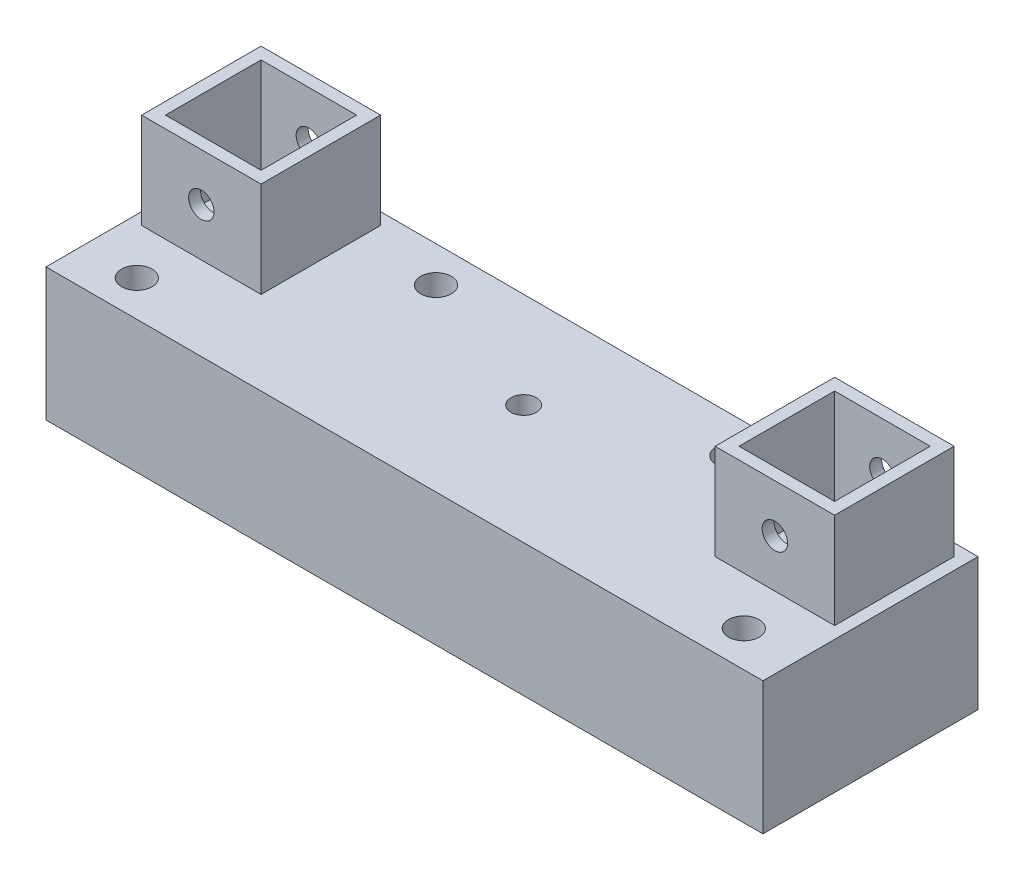
SolidWorks part; units mm, degrees
material "PPE"
ref_plane "Front Plane" through (0, 0, 0) normal (0, 0, 1) x (1, 0, 0)
ref_plane "Top Plane" through (0, 0, 0) normal (0, 1, 0) x (1, 0, 0)
ref_plane "Right Plane" through (0, 0, 0) normal (1, 0, 0) x (0, 0, -1)
sketch "Sketch1" plane through (0, 0, 0) normal (0, 1, 0) x (1, 0, 0)
  line L1 (-95.25, -28.575) -> (95.25, -28.575)
  line L2 (-95.25, -28.575) -> (-95.25, 28.575)
  line L3 (-95.25, 28.575) -> (95.25, 28.575)
  line L4 (95.25, -28.575) -> (95.25, 28.575)
  line L5 (-95.25, -28.575) -> (95.25, 28.575) construction
  line L6 (-95.25, 28.575) -> (95.25, -28.575) construction
  point P0 (0, 0)
  dimension "D1" = 190.5
  dimension "D2" = 57.15
extrude "Boss-Extrude1" add sketch "Sketch1" along normal blind 35.2298
sketch "Sketch2" plane through (0, 35.2298, 0) normal (0, 1, 0) x (1, 0, 0)
  line L1 (95.25, -28.575) -> (95.25, 28.575) construction
  line L2 (-95.25, -28.575) -> (95.25, -28.575) construction
  circle A0 centre (0, 3.0988) radius 3.3782
  dimension "D1" = 6.7564
  dimension "D2" = 95.25
  dimension "D3" = 31.6738
extrude "Cut-Extrude1" cut sketch "Sketch2" against normal blind 35.2298
sketch "Sketch3" plane through (0, 35.2298, 0) normal (0, 1, 0) x (1, 0, 0)
  line L1 (92.075, 25.4) -> (60.325, 25.4)
  line L2 (92.075, 25.4) -> (92.075, -6.35)
  line L3 (92.075, -6.35) -> (60.325, -6.35)
  line L4 (60.325, 25.4) -> (60.325, -6.35)
  line L5 (63.5, -3.175) -> (88.9, -3.175)
  line L6 (63.5, -3.175) -> (63.5, 22.225)
  line L7 (63.5, 22.225) -> (88.9, 22.225)
  line L8 (88.9, -3.175) -> (88.9, 22.225)
  line L10 (95.25, 28.575) -> (-95.25, 28.575) construction
  line L11 (95.25, -28.575) -> (95.25, 28.575) construction
  dimension "D1" = 31.75
  dimension "D2" = 31.75
  dimension "D3" = 25.4
  dimension "D4" = 25.4
  dimension "D5" = 3.175
  dimension "D6" = 3.175
  dimension "D7" = 3.175
  dimension "D8" = 3.175
extrude "Boss-Extrude2" add sketch "Sketch3" along normal blind 25.4
sketch "Sketch4" plane through (0, 0, -25.4) normal (0, 0, -1) x (-1, 0, 0)
  line L0 (-76.2, 60.6298) -> (-76.2, 35.2298) construction
  line L1 (-92.075, 60.6298) -> (-60.325, 60.6298) construction
  line L2 (-92.075, 35.2298) -> (-60.325, 35.2298) construction
  circle A0 centre (-76.2, 47.9298) radius 3.3782
  dimension "D1" = 6.7564
  dimension "D2" = 12.7
extrude "Cut-Extrude2" cut sketch "Sketch4" against normal through all
sketch "Sketch5" plane through (0, 0, 0) normal (0, -1, 0) x (1, 0, 0)
  line L0 (95.25, 28.575) -> (95.25, -28.575) construction
  line L1 (-95.25, 28.575) -> (95.25, 28.575) construction
  circle A0 centre (80.645, 19.05) radius 2.54
  circle A1 centre (39.243, -19.05) radius 2.54
  dimension "D6" = 5.08
  dimension "D1" = 14.605
  dimension "D2" = 9.525
  dimension "D4" = 47.625
  dimension "D5" = 56.007
extrude "Cut-Extrude3" cut sketch "Sketch5" against normal up to next (35.2298 mm away)
sketch "Sketch6" plane through (0, 35.2298, 0) normal (0, 1, 0) x (1, 0, 0)
  circle A0 centre (80.645, -19.05) radius 4.064
  circle A1 centre (39.243, 19.05) radius 4.064
  dimension "D1" = 8.128
extrude "Cut-Extrude4" cut sketch "Sketch6" against normal offset from surface (28.8798 mm away) 6.35 up to face at (80.645, 0, 16.51)
mirror "Mirror1" about plane through (0, 0, 0) normal (1, 0, 0) of "Cut-Extrude4", "Cut-Extrude3", "Boss-Extrude2", "Cut-Extrude2"
sketch "Sketch7" plane through (0, 0, 0) normal (0, -1, 0) x (1, 0, 0)
  line L0 (95.25, -28.575) -> (-95.25, -28.575) construction
  line L1 (6.5991, -3.0988) -> (3.2996, 2.6162)
  line L2 (3.2996, 2.6162) -> (-3.2996, 2.6162)
  line L3 (-3.2996, 2.6162) -> (-6.5991, -3.0988)
  line L4 (-6.5991, -3.0988) -> (-3.2996, -8.8138)
  line L5 (-3.2996, -8.8138) -> (3.2996, -8.8138)
  line L6 (3.2996, -8.8138) -> (6.5991, -3.0988)
  circle A0 centre (0, -3.0988) radius 5.715 construction
  dimension "D1" = 11.43
extrude "Cut-Extrude5" cut sketch "Sketch7" against normal offset from surface (9.8298 mm away) 25.4 up to face at (-80.645, 35.2298, 23.114)
scale "Scale1" [suppressed]
